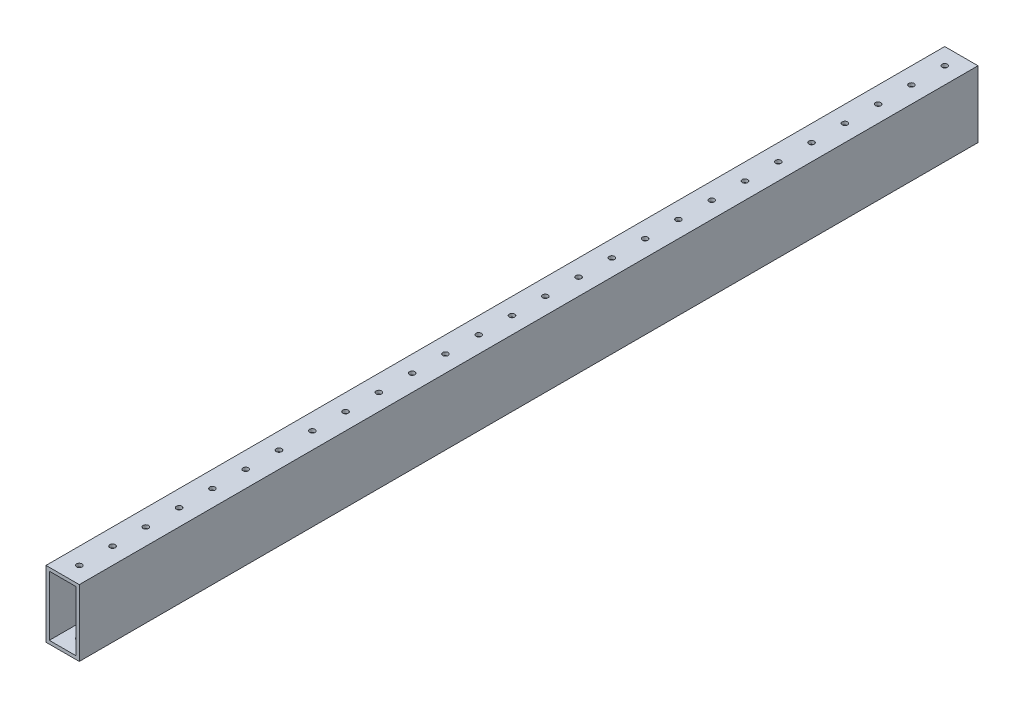
SolidWorks part; units mm, degrees
ref_plane "Front" through (0, 0, 0) normal (0, 0, 1) x (1, 0, 0)
ref_plane "Top" through (0, 0, 0) normal (0, 1, 0) x (1, 0, 0)
ref_plane "Right" through (0, 0, 0) normal (1, 0, 0) x (0, 0, -1)
sketch "Sketch1" plane through (0, 0, 0) normal (0, 0, 1) x (1, 0, 0)
  line L5 (-12.7, -25.4) -> (12.7, -25.4)
  line L6 (-12.7, -25.4) -> (-12.7, 25.4)
  line L7 (-12.7, 25.4) -> (12.7, 25.4)
  line L8 (12.7, -25.4) -> (12.7, 25.4)
  line L9 (-12.7, -25.4) -> (12.7, 25.4) construction
  line L10 (-12.7, 25.4) -> (12.7, -25.4) construction
  point P0 (0, 0)
  dimension "D1" = 50.8
  dimension "D2" = 25.4
extrude "Extrude-Thin1" add sketch "Sketch1" along normal mid plane 685.8 thin thin type one direction reverse wall 2.54
sketch "Sketch2" plane through (0, 25.4, 0) normal (0, 1, 0) x (1, 0, 0)
  line L0 (0, -342.9) -> (0, -330.2) construction
  line L1 (12.7, -342.9) -> (-12.7, -342.9) construction
  circle A0 centre (0, -330.2) radius 2.0701
  dimension "D1" = 4.1402
  dimension "D2" = 12.7
extrude "Cut-Extrude1" cut sketch "Sketch2" against normal through all
pattern_linear "LPattern1" count 28 spacing 25.4 along (0, 0, -1) of "Cut-Extrude1"
equation "\"lenght\"= 27"
equation "\"D1@Extrude-Thin1\"=\"lenght\""
equation "\"D1@LPattern1\"=\"lenght\"+1"
